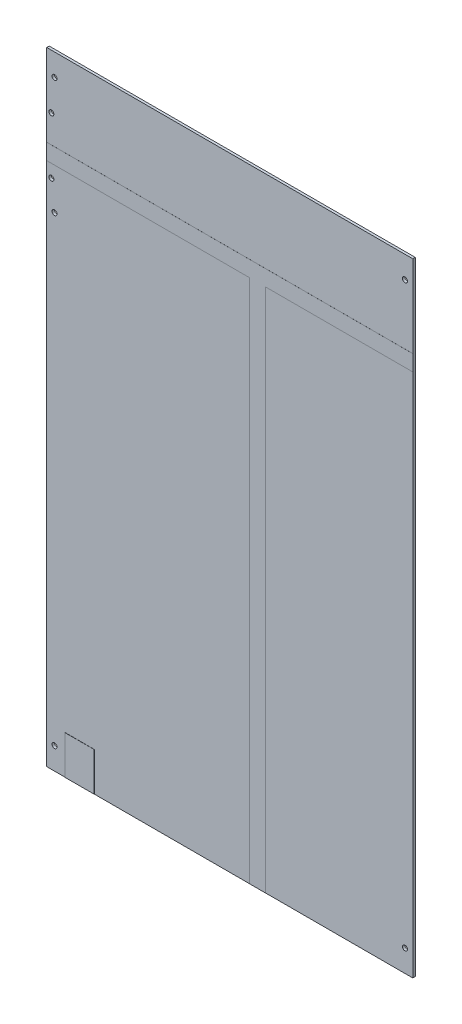
SolidWorks part; units mm, degrees
ref_plane "Front Plane" through (0, 0, 0) normal (0, 0, 1) x (1, 0, 0)
ref_plane "Top Plane" through (0, 0, 0) normal (0, 1, 0) x (1, 0, 0)
ref_plane "Right Plane" through (0, 0, 0) normal (1, 0, 0) x (0, 0, -1)
sketch "Sketch1" plane through (0, 0, 0) normal (0, 0, 1) x (1, 0, 0)
  line L1 (-117.2337, 57.658) -> (117.2337, 57.658)
  line L2 (-117.2337, 57.658) -> (-117.2337, -341.2617)
  line L3 (-117.2337, -341.2617) -> (117.2337, -341.2617)
  line L4 (117.2337, 57.658) -> (117.2337, -341.2617)
  dimension "D1" = 234.4674
  dimension "D2" = 398.9197
  dimension "D4" = 117.2337
  dimension "D3" = 57.658
extrude "Boss-Extrude1" add sketch "Sketch1" along normal blind 1.5875
sketch "Sketch3" plane through (0, 0, 1.5875) normal (0, 0, 1) x (1, 0, 0)
  line L0 (-117.2337, 0) -> (117.2337, 0)
  line L1 (-117.2337, 57.658) -> (-117.2337, -341.2617) construction
  line L2 (117.2337, -341.2617) -> (117.2337, 57.658) construction
  dimension "D1" = 0
sketch "Sketch4" plane through (0, 0, 1.5875) normal (0, 0, 1) x (1, 0, 0)
  line L0 (-117.2337, 57.658) -> (-117.2337, -341.2617) construction
  line L1 (-117.2337, 5.08) -> (117.2337, 5.08)
  line L2 (-117.2337, 5.08) -> (-117.2337, -5.08)
  line L4 (117.2337, 5.08) -> (117.2337, -5.08)
  line L5 (117.2337, -341.2617) -> (117.2337, 57.658) construction
  line L7 (-117.2337, -341.2617) -> (117.2337, -341.2617) construction
  line L9 (12.827, -5.08) -> (12.827, -341.2617)
  line L10 (12.827, -341.2617) -> (22.987, -341.2617)
  line L11 (22.987, -5.08) -> (22.987, -341.2617)
  line L13 (-117.2337, -5.08) -> (12.827, -5.08)
  line L14 (22.987, -5.08) -> (117.2337, -5.08)
  line L15 (-117.2337, 0) -> (117.2337, 0) construction
  point P16 (22.987, -173.1708)
  dimension "D3" = 10.16
  dimension "D1" = 10.16
  dimension "D2" = 5.08
  dimension "D4" = 10.16
  dimension "D5" = 22.987
extrude "Boss-Extrude2" add sketch "Sketch4" along normal blind 0.0254 and the other way blind 1.6254
sketch "Sketch5" plane through (0, 0, 1.5875) normal (0, 0, 1) x (1, 0, 0)
  line L0 (117.2337, 5.08) -> (117.2337, 57.658) construction
  line L1 (117.2337, 57.658) -> (-117.2337, 57.658) construction
  line L3 (22.987, -341.2617) -> (117.2337, -341.2617) construction
  line L4 (117.2337, -341.2617) -> (117.2337, -5.08) construction
  circle A1 centre (112.2337, 43.514) radius 1.6
  circle A3 centre (112.2337, -327.1177) radius 1.6
  dimension "D4" = 3.2
  dimension "D3" = 3.2
  dimension "D1" = 14.144
  dimension "D5" = 14.144
  dimension "D6" = 5
  dimension "D2" = 5
extrude "Cut-Extrude1" cut sketch "Sketch5" against normal through all
mirror "Mirror1" [suppressed] about plane through (0, 0, 0) normal (1, 0, 0)
mirror "Mirror2" [suppressed] about plane through (0, 0, 0) normal (0, 1, 0)
mirror "Mirror3" about plane through (0, 0, 0) normal (1, 0, 0) of "Cut-Extrude1"
sketch "Sketch6" plane through (0, 0, 1.5875) normal (0, 0, 1) x (1, 0, 0)
  line L0 (-117.2337, -341.2617) -> (12.827, -341.2617) construction
  line L1 (-86.729, -316.4596) -> (-105.295, -316.4596)
  line L2 (-86.729, -316.4596) -> (-86.729, -341.2617)
  line L3 (-86.729, -341.2617) -> (-105.295, -341.2617)
  line L4 (-105.295, -316.4596) -> (-105.295, -341.2617)
  line L5 (-86.729, -316.4596) -> (-105.295, -341.2617) construction
  line L6 (-86.729, -341.2617) -> (-105.295, -316.4596) construction
  line L7 (-117.2337, -5.08) -> (-117.2337, -341.2617) construction
  point P0 (-96.012, -328.8606)
  dimension "D1" = 21.2217
extrude "Boss-Extrude3" add sketch "Sketch6" along normal blind 0.1
sketch "Sketch7" plane through (0, 0, 1.5875) normal (0, 0, 1) x (1, 0, 0)
  line L0 (-117.2337, -5.08) -> (-117.2337, -341.2617) construction
  circle A0 centre (-112.2337, -31.486) radius 1.6
  dimension "D1" = 3.2
  dimension "D2" = 5
  dimension "D3" = 75
sketch "Sketch8" plane through (0, 0, 1.5875) normal (0, 0, 1) x (1, 0, 0)
  line L0 (-117.2337, 0) -> (117.2337, 0) construction
  line L1 (-117.2337, -5.08) -> (-117.2337, -341.2617) construction
  line L2 (-117.2337, 57.658) -> (-117.2337, 5.08) construction
  circle A0 centre (-114.2337, 22.8587) radius 1.6
  circle A1 centre (-114.2337, -13.3363) radius 1.6
  dimension "D1" = 3.2
  dimension "D2" = 3.2
  dimension "D3" = 22.8587
  dimension "D4" = 13.3363
  dimension "D5" = 3
  dimension "D6" = 3
extrude "Cut-Extrude2" cut sketch "Sketch8" against normal through all
extrude "Cut-Extrude3" cut sketch "Sketch7" against normal blind 10
equation "\"D4@Sketch1\"=\"D1@Sketch1\"/2"
equation "\"D3@Sketch4\"=\"D1@Sketch4\""
equation "\"D2@Sketch4\"=\"D1@Sketch4\"/2"
equation "\"D4@Sketch4\"=\"D1@Sketch4\""
equation "\"D3@Sketch5\"=\"D4@Sketch5\""
equation "\"D5@Sketch5\"=\"D1@Sketch5\""
equation "\"D6@Sketch5\"=\"D2@Sketch5\""
equation "\"D6@Sketch8\"=\"D5@Sketch8\""
